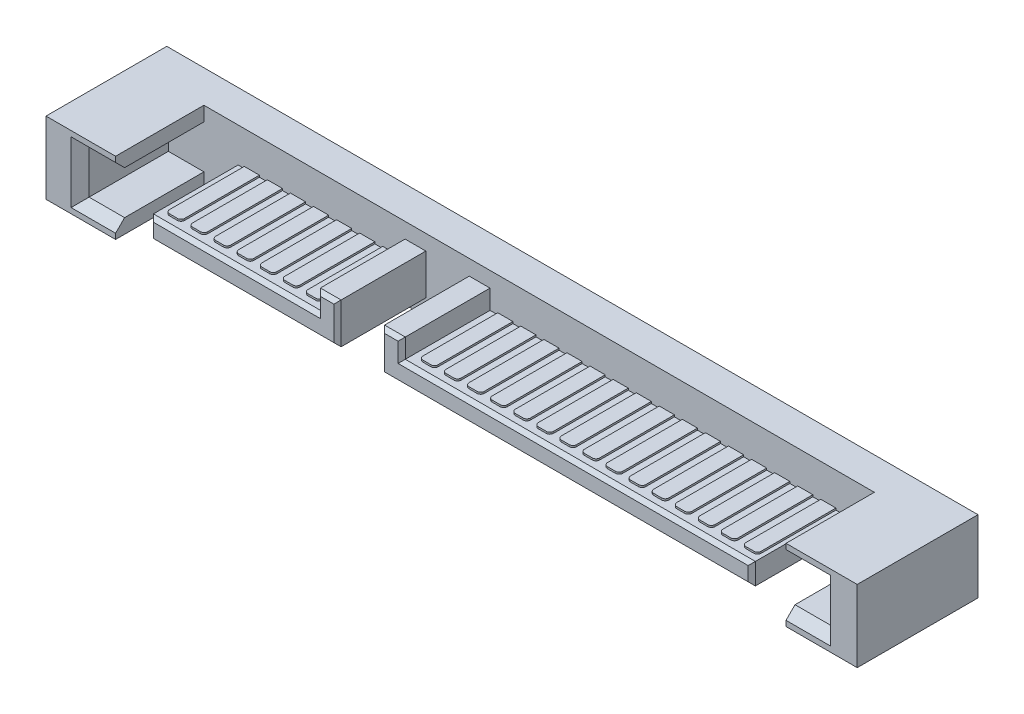
SolidWorks part; units mm, degrees
ref_plane "Front Plane" through (0, 0, 0) normal (0, 0, 1) x (1, 0, 0)
ref_plane "Top Plane" through (0, 0, 0) normal (0, 1, 0) x (1, 0, 0)
ref_plane "Right Plane" through (0, 0, 0) normal (1, 0, 0) x (0, 0, -1)
sketch "Sketch1" plane through (0, 0, 0) normal (0, 1, 0) x (1, 0, 0)
  line L1 (-22.5, -3.35) -> (22.5, -3.35)
  line L2 (-22.5, -3.35) -> (-22.5, 3.35)
  line L3 (-22.5, 3.35) -> (22.5, 3.35)
  line L4 (22.5, -3.35) -> (22.5, 3.35)
  line L5 (-22.5, -3.35) -> (22.5, 3.35) construction
  line L6 (-22.5, 3.35) -> (22.5, -3.35) construction
  point P0 (0, 0)
  dimension "D1" = 45
  dimension "D2" = 6.7
extrude "Boss-Extrude1" add sketch "Sketch1" along normal blind 4
sketch "Sketch2" plane through (0, 0, 3.35) normal (0, 0, 1) x (1, 0, 0)
  line L0 (-16.74, 2.08) -> (-16.74, 0.9)
  line L1 (-16.74, 0.9) -> (-6.33, 0.9)
  line L2 (-6.33, 0.9) -> (-6.33, 3.15)
  line L3 (-6.33, 3.15) -> (-7.48, 3.15)
  line L4 (-7.48, 3.15) -> (-7.48, 2.08)
  line L5 (-7.48, 2.08) -> (-16.74, 2.08)
  line L6 (-3.92, 0.9) -> (16.65, 0.9)
  line L7 (16.65, 0.9) -> (16.65, 2.08)
  line L8 (16.65, 2.08) -> (-2.77, 2.08)
  line L9 (-2.77, 2.08) -> (-2.77, 3.15)
  line L10 (-2.77, 3.15) -> (-3.92, 3.15)
  line L11 (-3.92, 3.15) -> (-3.92, 0.9)
  line L12 (-22.5, 4) -> (22.5, 4) construction
  line L13 (22.5, 4) -> (22.5, 0) construction
  line L15 (-18.64, 7.2726) -> (18.55, 7.2726)
  line L20 (-18.64, 7.2726) -> (-18.64, 0)
  line L21 (-18.64, 0) -> (18.55, 0)
  line L22 (18.55, 7.2726) -> (18.55, 0)
  line L23 (-18.64, 0.8) -> (-20.61, 0.8)
  line L24 (-18.64, 0.8) -> (-18.64, 3.2)
  line L25 (-18.64, 3.2) -> (-20.61, 3.2)
  line L26 (-20.61, 0.8) -> (-20.61, 3.2)
  line L27 (18.55, 0.8) -> (20.52, 0.8)
  line L28 (18.55, 0.8) -> (18.55, 3.2)
  line L29 (18.55, 3.2) -> (20.52, 3.2)
  line L30 (20.52, 0.8) -> (20.52, 3.2)
  line M26 (-22.5, 0) -> (22.5, 0)
  line M28 (22.5, 4) -> (-22.5, 4)
  dimension "D1" = 0.85
  dimension "D2" = 0.85
  dimension "D3" = 2.41
  dimension "D4" = 1.15
  dimension "D5" = 1.15
  dimension "D6" = 9.26
  dimension "D7" = 19.42
  dimension "D8" = 5.85
  dimension "D9" = 1.18
  dimension "D10" = 1.18
  dimension "D11" = 1.07
  dimension "D12" = 1.9
  dimension "D13" = 1.9
  dimension "D14" = 0.9
  dimension "D15" = 3.87
  dimension "D16" = 3.87
  dimension "D17" = 0.1
  dimension "D18" = 0.1
  dimension "D19" = 2.4
  dimension "D20" = 2.4
extrude "Cut-Extrude1" cut sketch "Sketch2" against normal blind 4.9 contours L26 L23 L20 L25 | L22 L20 L11 L10 L9 L8 L7 L6 L5 L4 L3 L2 L1 L0 M28 M26 | L27 L30 L29 L22
sketch "Sketch3" plane through (0, 2.08, 0) normal (0, 1, 0) x (1, 0, 0)
  line L0 (18.55, 1.55) -> (-18.64, 1.55) construction
  line L1 (-7.88, 1.55) -> (-8.72, 1.55)
  line L2 (-7.88, 1.55) -> (-7.88, -2.6)
  line L3 (-8.08, -2.8) -> (-8.52, -2.8)
  line L4 (-8.72, 1.55) -> (-8.72, -2.6)
  line L5 (-7.48, 1.55) -> (-7.48, -3.35) construction
  line L6 (-9.16, 1.55) -> (-9.16, -2.6)
  line L7 (-9.16, 1.55) -> (-10, 1.55)
  line L8 (-10, 1.55) -> (-10, -2.6)
  line L9 (-9.36, -2.8) -> (-9.8, -2.8)
  line L10 (-10.44, 1.55) -> (-10.44, -2.6)
  line L11 (-10.44, 1.55) -> (-11.28, 1.55)
  line L12 (-11.28, 1.55) -> (-11.28, -2.6)
  line L13 (-10.64, -2.8) -> (-11.08, -2.8)
  line L14 (-11.72, 1.55) -> (-11.72, -2.6)
  line L15 (-11.72, 1.55) -> (-12.56, 1.55)
  line L16 (-12.56, 1.55) -> (-12.56, -2.6)
  line L17 (-11.92, -2.8) -> (-12.36, -2.8)
  line L18 (-13, 1.55) -> (-13, -2.6)
  line L19 (-13, 1.55) -> (-13.84, 1.55)
  line L20 (-13.84, 1.55) -> (-13.84, -2.6)
  line L21 (-13.2, -2.8) -> (-13.64, -2.8)
  line L22 (-14.28, 1.55) -> (-14.28, -2.6)
  line L23 (-14.28, 1.55) -> (-15.12, 1.55)
  line L24 (-15.12, 1.55) -> (-15.12, -2.6)
  line L25 (-14.48, -2.8) -> (-14.92, -2.8)
  line L26 (-15.56, 1.55) -> (-15.56, -2.6)
  line L27 (-15.56, 1.55) -> (-16.4, 1.55)
  line L28 (-16.4, 1.55) -> (-16.4, -2.6)
  line L29 (-15.76, -2.8) -> (-16.2, -2.8)
  line L30 (16.65, 1.55) -> (-2.77, 1.55) construction
  line L31 (-2.34, 1.55) -> (-1.5, 1.55)
  line L32 (-2.34, 1.55) -> (-2.34, -2.6)
  line L33 (-2.14, -2.8) -> (-1.7, -2.8)
  line L34 (-1.5, 1.55) -> (-1.5, -2.6)
  line L35 (-2.77, 1.55) -> (-2.77, -3.35) construction
  line L36 (-1.06, 1.55) -> (-1.06, -2.6)
  line L37 (-1.06, 1.55) -> (-0.22, 1.55)
  line L38 (-0.22, 1.55) -> (-0.22, -2.6)
  line L39 (-0.86, -2.8) -> (-0.42, -2.8)
  line L40 (0.22, 1.55) -> (0.22, -2.6)
  line L41 (0.22, 1.55) -> (1.06, 1.55)
  line L42 (1.06, 1.55) -> (1.06, -2.6)
  line L43 (0.42, -2.8) -> (0.86, -2.8)
  line L44 (1.5, 1.55) -> (1.5, -2.6)
  line L45 (1.5, 1.55) -> (2.34, 1.55)
  line L46 (2.34, 1.55) -> (2.34, -2.6)
  line L47 (1.7, -2.8) -> (2.14, -2.8)
  line L48 (2.78, 1.55) -> (2.78, -2.6)
  line L49 (2.78, 1.55) -> (3.62, 1.55)
  line L50 (3.62, 1.55) -> (3.62, -2.6)
  line L51 (2.98, -2.8) -> (3.42, -2.8)
  line L52 (4.06, 1.55) -> (4.06, -2.6)
  line L53 (4.06, 1.55) -> (4.9, 1.55)
  line L54 (4.9, 1.55) -> (4.9, -2.6)
  line L55 (4.26, -2.8) -> (4.7, -2.8)
  line L56 (5.34, 1.55) -> (5.34, -2.6)
  line L57 (5.34, 1.55) -> (6.18, 1.55)
  line L58 (6.18, 1.55) -> (6.18, -2.6)
  line L59 (5.54, -2.8) -> (5.98, -2.8)
  line L60 (6.62, 1.55) -> (6.62, -2.6)
  line L61 (6.62, 1.55) -> (7.46, 1.55)
  line L62 (7.46, 1.55) -> (7.46, -2.6)
  line L63 (6.82, -2.8) -> (7.26, -2.8)
  line L64 (7.9, 1.55) -> (7.9, -2.6)
  line L65 (7.9, 1.55) -> (8.74, 1.55)
  line L66 (8.74, 1.55) -> (8.74, -2.6)
  line L67 (8.1, -2.8) -> (8.54, -2.8)
  line L68 (9.18, 1.55) -> (9.18, -2.6)
  line L69 (9.18, 1.55) -> (10.02, 1.55)
  line L70 (10.02, 1.55) -> (10.02, -2.6)
  line L71 (9.38, -2.8) -> (9.82, -2.8)
  line L72 (10.46, 1.55) -> (10.46, -2.6)
  line L73 (10.46, 1.55) -> (11.3, 1.55)
  line L74 (11.3, 1.55) -> (11.3, -2.6)
  line L75 (10.66, -2.8) -> (11.1, -2.8)
  line L76 (11.74, 1.55) -> (11.74, -2.6)
  line L77 (11.74, 1.55) -> (12.58, 1.55)
  line L78 (12.58, 1.55) -> (12.58, -2.6)
  line L79 (11.94, -2.8) -> (12.38, -2.8)
  line L80 (13.02, 1.55) -> (13.02, -2.6)
  line L81 (13.02, 1.55) -> (13.86, 1.55)
  line L82 (13.86, 1.55) -> (13.86, -2.6)
  line L83 (13.22, -2.8) -> (13.66, -2.8)
  line L84 (14.3, 1.55) -> (14.3, -2.6)
  line L85 (14.3, 1.55) -> (15.14, 1.55)
  line L86 (15.14, 1.55) -> (15.14, -2.6)
  line L87 (14.5, -2.8) -> (14.94, -2.8)
  line L88 (15.58, 1.55) -> (15.58, -2.6)
  line L89 (15.58, 1.55) -> (16.42, 1.55)
  line L90 (16.42, 1.55) -> (16.42, -2.6)
  line L91 (15.78, -2.8) -> (16.22, -2.8)
  arc A0 (-7.88, -2.6) -> (-8.08, -2.8) centre (-8.08, -2.6) cw
  arc A1 (-8.52, -2.8) -> (-8.72, -2.6) centre (-8.52, -2.6) cw
  arc A2 (-9.16, -2.6) -> (-9.36, -2.8) centre (-9.36, -2.6) cw
  arc A3 (-9.8, -2.8) -> (-10, -2.6) centre (-9.8, -2.6) cw
  arc A4 (-10.44, -2.6) -> (-10.64, -2.8) centre (-10.64, -2.6) cw
  arc A5 (-11.08, -2.8) -> (-11.28, -2.6) centre (-11.08, -2.6) cw
  arc A6 (-11.72, -2.6) -> (-11.92, -2.8) centre (-11.92, -2.6) cw
  arc A7 (-12.36, -2.8) -> (-12.56, -2.6) centre (-12.36, -2.6) cw
  arc A8 (-13, -2.6) -> (-13.2, -2.8) centre (-13.2, -2.6) cw
  arc A9 (-13.64, -2.8) -> (-13.84, -2.6) centre (-13.64, -2.6) cw
  arc A10 (-14.28, -2.6) -> (-14.48, -2.8) centre (-14.48, -2.6) cw
  arc A11 (-14.92, -2.8) -> (-15.12, -2.6) centre (-14.92, -2.6) cw
  arc A12 (-15.56, -2.6) -> (-15.76, -2.8) centre (-15.76, -2.6) cw
  arc A13 (-16.2, -2.8) -> (-16.4, -2.6) centre (-16.2, -2.6) cw
  arc A14 (-1.7, -2.8) -> (-1.5, -2.6) centre (-1.7, -2.6) ccw
  arc A15 (-2.34, -2.6) -> (-2.14, -2.8) centre (-2.14, -2.6) ccw
  arc A16 (-1.06, -2.6) -> (-0.86, -2.8) centre (-0.86, -2.6) ccw
  arc A17 (-0.42, -2.8) -> (-0.22, -2.6) centre (-0.42, -2.6) ccw
  arc A18 (0.22, -2.6) -> (0.42, -2.8) centre (0.42, -2.6) ccw
  arc A19 (0.86, -2.8) -> (1.06, -2.6) centre (0.86, -2.6) ccw
  arc A20 (1.5, -2.6) -> (1.7, -2.8) centre (1.7, -2.6) ccw
  arc A21 (2.14, -2.8) -> (2.34, -2.6) centre (2.14, -2.6) ccw
  arc A22 (2.78, -2.6) -> (2.98, -2.8) centre (2.98, -2.6) ccw
  arc A23 (3.42, -2.8) -> (3.62, -2.6) centre (3.42, -2.6) ccw
  arc A24 (4.06, -2.6) -> (4.26, -2.8) centre (4.26, -2.6) ccw
  arc A25 (4.7, -2.8) -> (4.9, -2.6) centre (4.7, -2.6) ccw
  arc A26 (5.34, -2.6) -> (5.54, -2.8) centre (5.54, -2.6) ccw
  arc A27 (5.98, -2.8) -> (6.18, -2.6) centre (5.98, -2.6) ccw
  arc A28 (6.62, -2.6) -> (6.82, -2.8) centre (6.82, -2.6) ccw
  arc A29 (7.26, -2.8) -> (7.46, -2.6) centre (7.26, -2.6) ccw
  arc A30 (7.9, -2.6) -> (8.1, -2.8) centre (8.1, -2.6) ccw
  arc A31 (8.54, -2.8) -> (8.74, -2.6) centre (8.54, -2.6) ccw
  arc A32 (9.18, -2.6) -> (9.38, -2.8) centre (9.38, -2.6) ccw
  arc A33 (9.82, -2.8) -> (10.02, -2.6) centre (9.82, -2.6) ccw
  arc A34 (10.46, -2.6) -> (10.66, -2.8) centre (10.66, -2.6) ccw
  arc A35 (11.1, -2.8) -> (11.3, -2.6) centre (11.1, -2.6) ccw
  arc A36 (11.74, -2.6) -> (11.94, -2.8) centre (11.94, -2.6) ccw
  arc A37 (12.38, -2.8) -> (12.58, -2.6) centre (12.38, -2.6) ccw
  arc A38 (13.02, -2.6) -> (13.22, -2.8) centre (13.22, -2.6) ccw
  arc A39 (13.66, -2.8) -> (13.86, -2.6) centre (13.66, -2.6) ccw
  arc A40 (14.3, -2.6) -> (14.5, -2.8) centre (14.5, -2.6) ccw
  arc A41 (14.94, -2.8) -> (15.14, -2.6) centre (14.94, -2.6) ccw
  arc A42 (15.58, -2.6) -> (15.78, -2.8) centre (15.78, -2.6) ccw
  arc A43 (16.22, -2.8) -> (16.42, -2.6) centre (16.22, -2.6) ccw
  point P8 (-7.88, -2.8)
  point P11 (-8.72, -2.8)
  point P72 (-1.5, -2.8)
  point P75 (-2.34, -2.8)
  dimension "D3" = 0.2
  dimension "D8" = 0.2
  dimension "D1" = 0.84
  dimension "D2" = 4.35
  dimension "D4" = 0.4
  dimension "D6" = 0.84
  dimension "D7" = 0.43
  dimension "D5" = 7
  dimension "D9" = 15
extrude "Boss-Extrude2" add sketch "Sketch3" along normal blind 0.1
chamfer "Chamfer1" distance 0.5 angle 45 6 edges at (19.535, 3.2, 3.35) (20.52, 2, 3.35) (19.535, 0.8, 3.35) (-19.625, 3.2, 3.35) (-20.61, 2, 3.35) (-19.625, 0.8, 3.35)
chamfer "Chamfer2" distance 0.2 angle 45 12 edges at (-7.48, 2.615, 3.35) (-6.905, 3.15, 3.35) (-6.33, 2.025, 3.35) (-11.535, 0.9, 3.35) (-16.74, 1.49, 3.35) (-12.11, 2.08, 3.35) (-3.345, 3.15, 3.35) (-2.77, 2.615, 3.35) (6.94, 2.08, 3.35) (16.65, 1.49, 3.35) (6.365, 0.9, 3.35) (-3.92, 2.025, 3.35)
